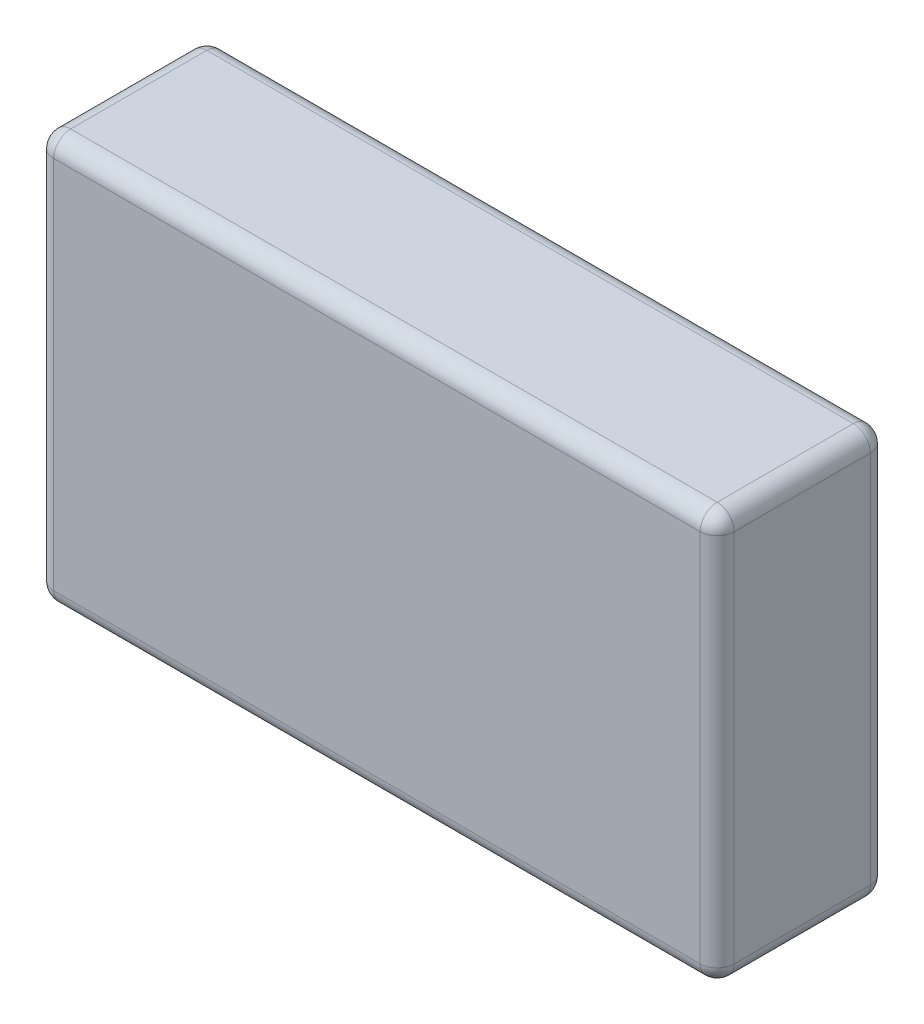
SolidWorks part; units mm, degrees
ref_plane "正面" through (0, 0, 0) normal (0, 0, 1) x (1, 0, 0)
ref_plane "平面" through (0, 0, 0) normal (0, 1, 0) x (1, 0, 0)
ref_plane "右側面" through (0, 0, 0) normal (1, 0, 0) x (0, 0, -1)
sketch "ｽｹｯﾁ1" plane through (0, 0, 0) normal (0, 0, 1) x (1, 0, 0)
  line L1 (-10, -6) -> (10, -6)
  line L2 (-10, -6) -> (-10, 6)
  line L3 (-10, 6) -> (10, 6)
  line L4 (10, -6) -> (10, 6)
  line L5 (-10, -6) -> (10, 6) construction
  line L6 (-10, 6) -> (10, -6) construction
  point P0 (0, 0)
  dimension "D1" = 20
  dimension "D2" = 12
extrude "ﾎﾞｽ - 押し出し1" add sketch "ｽｹｯﾁ1" along normal blind 5
fillet "ﾌｨﾚｯﾄ1" radius 0.5 12 edges at (0, 6, 0) (-10, 0, 0) (0, -6, 0) (10, 0, 0) (0, -6, 5) (-10, 0, 5) (0, 6, 5) (10, 0, 5) (-10, -6, 2.5) (10, -6, 2.5) (10, 6, 2.5) (-10, 6, 2.5)
